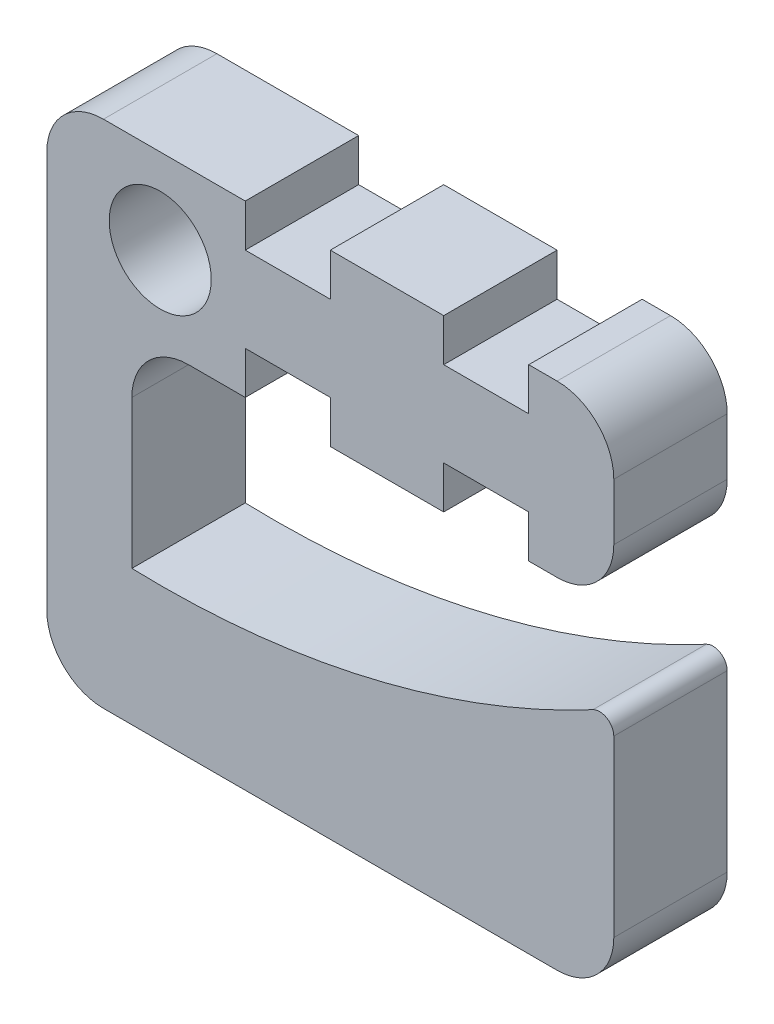
SolidWorks part; units mm, degrees
ref_plane "Front Plane" through (0, 0, 0) normal (0, 0, 1) x (1, 0, 0)
ref_plane "Top Plane" through (0, 0, 0) normal (0, 1, 0) x (1, 0, 0)
ref_plane "Right Plane" through (0, 0, 0) normal (1, 0, 0) x (0, 0, -1)
sketch "Sketch2" plane through (0, 0, 0) normal (0, 0, 1) x (1, 0, 0)
  line L0 (20.32, -12.7) -> (20.32, -7.62)
  line L1 (20.32, -3.81) -> (-5.08, -3.81)
  line L2 (20.32, -3.81) -> (20.32, 3.81)
  line L3 (20.32, 3.81) -> (-5.08, 3.81)
  line L4 (-5.08, -3.81) -> (-5.08, 3.81)
  line L5 (-5.08, -3.81) -> (-1.27, -3.81)
  line L6 (-5.08, -3.81) -> (-5.08, -19.05)
  line L7 (-5.08, -19.05) -> (-1.27, -19.05)
  line L8 (-1.27, -3.81) -> (-1.27, -19.05)
  line L9 (-1.27, -19.05) -> (20.32, -19.05)
  line L10 (-1.27, -19.05) -> (-1.27, -12.7)
  line L11 (-1.27, -12.7) -> (20.32, -12.7)
  line L12 (20.32, -19.05) -> (20.32, -12.7)
  circle A0 centre (0, 0) radius 2.286
  arc A1 (20.32, -7.62) -> (-20.32, -7.62) centre (0, 28.0426) cw
  point P7 (20.32, 0)
  point P17 (0, 69.088)
  point P18 (-12.5601, -9.3747)
  point P19 (0, -13.0028)
  point P20 (-15.24, -8.89)
  dimension "D1" = 4.572
  dimension "D2" = 25.4
  dimension "D3" = 7.62
  dimension "D4" = 5.08
  dimension "D5" = 1.27
  dimension "D6" = 15.24
  dimension "D7" = 6.35
  dimension "D8" = 5.08
extrude "Boss-Extrude1" add sketch "Sketch2" along normal blind 5.08 contours L4 L1 L2 L3 A0 | A1 L8 L1 L6 | L8 A1 L6 L7 | L9 L12 L11 L8 | L0 A1 L8 L11
fillet "Fillet1" radius 2.54 6 edges at (20.32, -19.05, 2.54) (-5.08, -19.05, 2.54) (-5.08, 3.81, 2.54) (20.32, 3.81, 2.54) (20.32, -3.81, 2.54) (-1.27, -3.81, 2.54)
fillet "Fillet2" radius 0.635 1 edges at (20.32, -7.62, 2.54)
sketch "Sketch3" plane through (0, 0, 5.08) normal (0, 0, 1) x (1, 0, 0)
  line L0 (17.78, 3.81) -> (-2.54, 3.81) construction
  line L1 (3.81, 3.81) -> (7.62, 3.81)
  line L2 (3.81, 3.81) -> (3.81, 1.905)
  line L3 (3.81, 1.905) -> (7.62, 1.905)
  line L4 (7.62, 3.81) -> (7.62, 1.905)
  line L5 (10.16, 3.81) -> (10.16, -3.81) construction
  line L6 (17.78, -3.81) -> (1.27, -3.81) construction
  line L7 (0, 0) -> (20.32, 0) construction
  line L8 (20.32, -1.27) -> (20.32, 1.27) construction
  line L9 (3.81, -1.905) -> (7.62, -1.905)
  line L10 (7.62, -3.81) -> (7.62, -1.905)
  line L11 (3.81, -3.81) -> (3.81, -1.905)
  line L12 (16.51, -3.81) -> (16.51, -1.905)
  line L13 (12.7, -3.81) -> (12.7, -1.905)
  line L14 (16.51, -1.905) -> (12.7, -1.905)
  line L15 (12.7, 3.81) -> (12.7, 1.905)
  line L16 (16.51, 1.905) -> (12.7, 1.905)
  line L17 (16.51, 3.81) -> (16.51, 1.905)
  line M16 (1.27, -3.81) -> (17.78, -3.81)
  line M20 (17.78, 3.81) -> (-2.54, 3.81)
  dimension "D1" = 1.905
  dimension "D2" = 3.81
  dimension "D3" = 10.16
  dimension "D4" = 2.54
extrude "Cut-Extrude1" cut sketch "Sketch3" against normal through all contours L4 L2 L3 M20 | L11 L10 L9 M16 | L17 L15 L16 M20 | L12 L14 L13 M16
